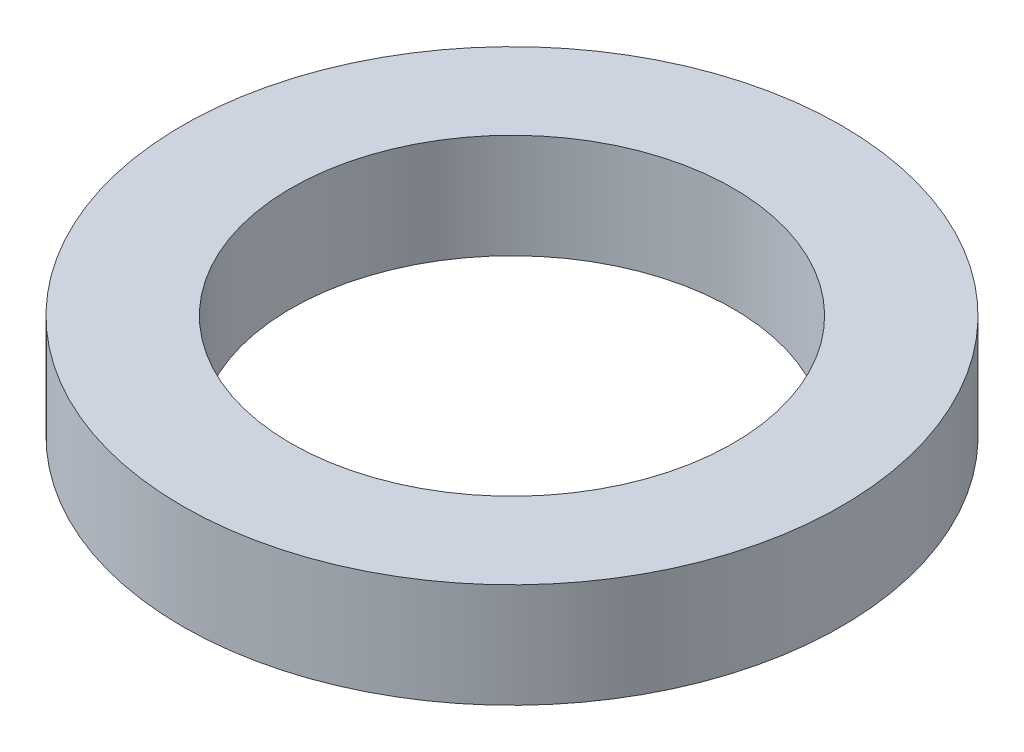
SolidWorks part; units mm, degrees
material "Aleación 1060"
ref_plane "Alzado" through (0, 0, 0) normal (0, 0, 1) x (1, 0, 0)
ref_plane "Planta" through (0, 0, 0) normal (0, 1, 0) x (1, 0, 0)
ref_plane "Vista lateral" through (0, 0, 0) normal (1, 0, 0) x (0, 0, -1)
sketch "Croquis1" plane through (0, 0, 0) normal (0, 1, 0) x (1, 0, 0)
  circle A0 centre (0, 0) radius 6
  circle A1 centre (0, 0) radius 4.025
  dimension "D1" = 12
  dimension "D2" = 8.05
extrude "Saliente-Extruir1" add sketch "Croquis1" along normal mid plane 1.9
